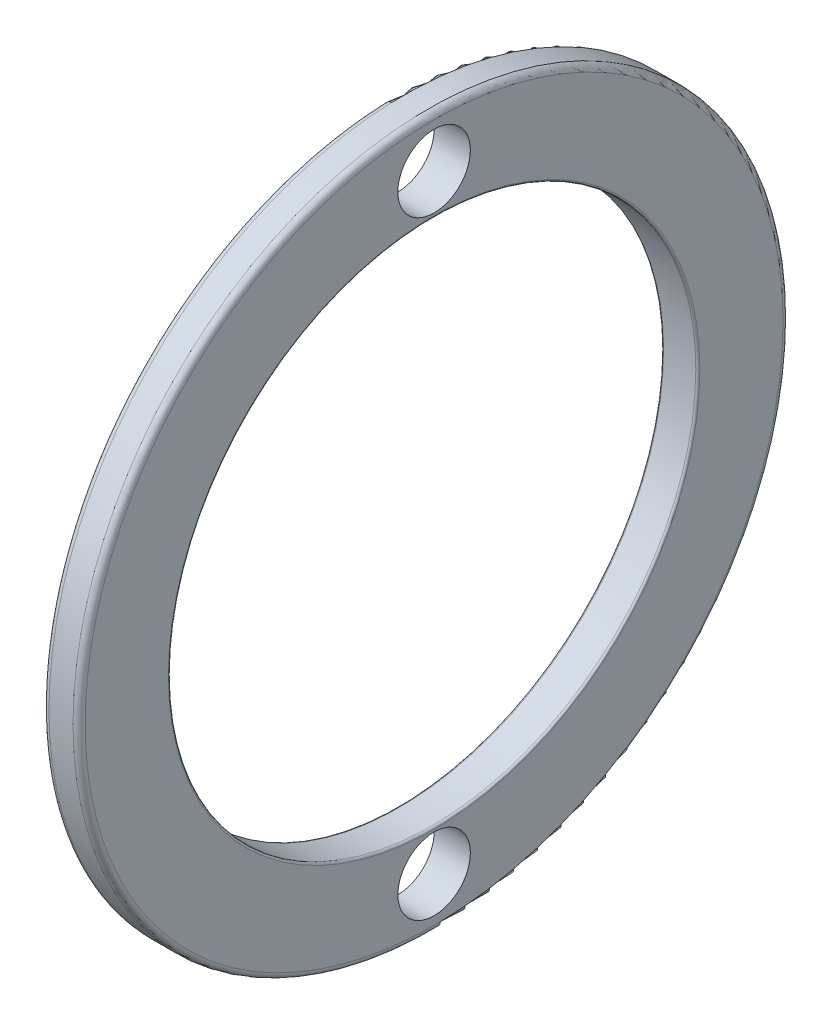
SolidWorks part; units mm, degrees
ref_plane "Alzado" through (0, 0, 0) normal (0, 0, 1) x (1, 0, 0)
ref_plane "Planta" through (0, 0, 0) normal (0, 1, 0) x (1, 0, 0)
ref_plane "Vista lateral" through (0, 0, 0) normal (1, 0, 0) x (0, 0, -1)
ref_plane "Plano1" through (0, 0, 0) normal (0, 0, 1) x (1, 0, 0)
sketch "Croquis1" plane through (0, 0, 0) normal (0, 0, 1) x (1, 0, 0)
  line L0 (5.214, 34.4) -> (5.214, 26.2)
  line L1 (5.414, 26) -> (8.586, 26)
  line L2 (8.786, 26.2) -> (8.786, 34.4)
  line L3 (8.186, 35) -> (5.814, 35)
  line L4 (50, 0) -> (-50, 0) construction
  arc A0 (5.214, 26.2) -> (5.414, 26) centre (5.414, 26.2) ccw
  arc A1 (8.586, 26) -> (8.786, 26.2) centre (8.586, 26.2) ccw
  arc A2 (8.786, 34.4) -> (8.186, 35) centre (8.186, 34.4) ccw
  arc A3 (5.814, 35) -> (5.214, 34.4) centre (5.814, 34.4) ccw
revolve "Revolución1" add sketch "Croquis1" angle 360 about L4
ref_plane "Plano2" through (0, 0, 0) normal (1, 0, 0) x (0, 0, -1)
sketch "Croquis2" plane through (0, 0, 0) normal (1, 0, 0) x (0, 0, -1)
  circle A0 centre (0, 30) radius 3.572
extrude "Extruir1" cut sketch "Croquis2" along normal blind 12.358
ref_plane "Plano3" through (0, 0, 0) normal (1, 0, 0) x (0, 0, -1)
sketch "Croquis3" plane through (0, 0, 0) normal (1, 0, 0) x (0, 0, -1)
  circle A0 centre (0, -30) radius 3.572
extrude "Extruir2" cut sketch "Croquis3" along normal blind 12.358
